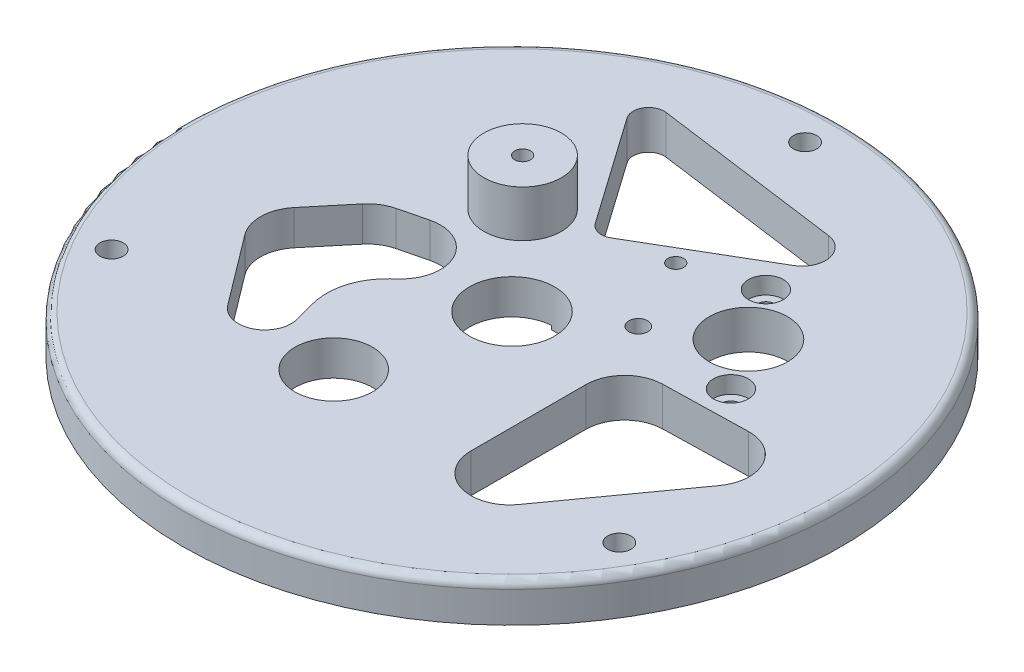
SolidWorks part; units mm, degrees
ref_plane "Front Plane" through (0, 0, 0) normal (0, 0, 1) x (1, 0, 0)
ref_plane "Top Plane" through (0, 0, 0) normal (0, 1, 0) x (1, 0, 0)
ref_plane "Right Plane" through (0, 0, 0) normal (1, 0, 0) x (0, 0, -1)
sketch "Sketch1" plane through (0, 0, 0) normal (0, 1, 0) x (1, 0, 0)
  circle A0 centre (0, 0) radius 42.5
  circle A9 centre (-5.0091, -17.9813) radius 5
  dimension "D1" = 85
  dimension "D5" = 10
  dimension "D6" = 18.666
extrude "Boss-Extrude1" add sketch "Sketch1" along normal blind 5
sketch "Sketch2" plane through (0, 5, 0) normal (0, 1, 0) x (1, 0, 0)
  line L0 (22.7613, 5.4702) -> (13.9311, 18.8129) construction
  line L1 (22.7613, 5.4702) -> (9.8011, 6.4864) construction
  line L2 (9.8011, 6.4864) -> (13.9311, 18.8129) construction
  line L3 (9.8011, 6.4864) -> (18.3462, 12.1416) construction
  circle A0 centre (22.7613, 5.4702) radius 1.2
  circle A1 centre (13.9311, 18.8129) radius 1.2
  circle A2 centre (9.8011, 6.4864) radius 1.225
  circle A3 centre (18.3462, 12.1416) radius 5.05
  circle A4 centre (5.1411, 15.9741) radius 1.015
  circle A5 centre (18.3462, 12.1416) radius 13.75 construction
  circle A6 centre (0, 0) radius 30 construction
  circle A7 centre (5.1411, 15.9741) radius 11.25 construction
  point P9 (18.3462, 12.1416)
  dimension "D1" = 2.4
  dimension "D2" = 10.1
  dimension "D3" = 2.45
  dimension "D7" = 2.03
  dimension "D9" = 60
  dimension "D10" = 22.5
  dimension "D4" = 16
  dimension "D5" = 13
  dimension "D6" = 22
  dimension "D8" = 13.75
extrude "Cut-Extrude1" cut sketch "Sketch2" against normal blind 10
sketch "Sketch4" plane through (0, 5, 0) normal (0, 1, 0) x (1, 0, 0)
  circle A0 centre (0, 0) radius 31 construction
  dimension "D1" = 62
sketch "Sketch5" plane through (0, 5, 0) normal (0, 1, 0) x (1, 0, 0)
  line L0 (-10.7483, 12.1208) -> (0, 0) construction
  circle A0 centre (-10.7483, 12.1208) radius 5
  circle A1 centre (5.1411, 15.9741) radius 1 construction
  circle A2 centre (-10.7483, 12.1208) radius 1.015
  circle A3 centre (-10.7483, 12.1208) radius 14 construction
  dimension "D2" = 10
  dimension "D3" = 2.03
  dimension "D4" = 28
  dimension "D1" = 16.35
  dimension "D5" = 16.2
extrude "Boss-Extrude2" add sketch "Sketch5" along normal blind 6
sketch "Sketch9" plane through (0, 0, 0) normal (0, -1, 0) x (1, 0, 0)
  circle A0 centre (5.1411, -15.9741) radius 2.3573
extrude "Boss-Extrude4" add sketch "Sketch9" against normal blind 1
fillet "Fillet1" radius 1 1 edges at (0, 5, 42.5)
sketch "Sketch10" plane through (0, 5, 0) normal (0, 1, 0) x (1, 0, 0)
  line L0 (-32.7358, -18.9) -> (0, 0) construction
  line L1 (0, 37.8) -> (0, 0) construction
  line L2 (32.7358, -18.9) -> (0, 0) construction
  circle A0 centre (0, 37.8) radius 1.5
  circle A1 centre (-32.7358, -18.9) radius 1.5
  circle A2 centre (32.7358, -18.9) radius 1.5
  dimension "D2" = 3
  dimension "D3" = 120
  dimension "D1" = 37.8
  dimension "D4" = 120
extrude "Cut-Extrude3" cut sketch "Sketch10" against normal blind 16 and the other way blind 2.2
sketch "Sketch12" plane through (0, 0, 0) normal (0, -1, 0) x (1, 0, 0)
  line L0 (-18.749, 25.6831) -> (-31.974, 2.7768)
  line L1 (-30.1438, -4.0534) -> (-11.5243, -14.8034)
  line L2 (-4.6942, -12.9732) -> (8.5308, 9.9331)
  line L3 (8.5308, 9.9331) -> (-18.749, 25.6831) construction
  line L4 (-5.1091, 17.8081) -> (-5.0091, 17.9813) construction
  line L5 (-32.7358, 18.9) -> (-36.8061, 21.25) construction
  line L6 (-25.1829, 14.5393) -> (-32.7358, 18.9) construction
  line L7 (-35.4958, 23.5194) -> (-39.334, 16.8715) construction
  arc A0 (-18.749, 25.6831) -> (8.5308, 9.9331) centre (-5.1091, 17.8081) cw
  arc A1 (-4.6942, -12.9732) -> (-11.5243, -14.8034) centre (-9.0243, -10.4732) cw
  arc A2 (-31.974, 2.7768) -> (-30.1438, -4.0534) centre (-27.6438, 0.2768) ccw
  circle A3 centre (-5.0091, 17.9813) radius 4.1018 construction
  circle A4 centre (-5.0091, 17.9813) radius 5 construction
  circle A5 centre (0, 0) radius 42.5 construction
  point P4 (2.7659, 31.448)
  point P9 (-7.1942, -17.3034)
  point P12 (-34.474, -1.5534)
  point P24 (0, 0)
  point P25 (-27.6438, 0)
  point P26 (-27.6438, 0)
  dimension "D3" = 5
  dimension "D4" = 0.2
  dimension "D1" = 47.2
  dimension "D2" = 31.5
extrude "Cut-Extrude6" cut sketch "Sketch12" against normal blind 0.5
sketch "Sketch13" plane through (0, 5, 0) normal (0, 1, 0) x (1, 0, 0)
  line L0 (32.8168, -6.0717) -> (21.985, -21.1386)
  line L1 (12.9252, -18.2178) -> (12.9317, -3.4072)
  line L2 (17.8133, 1.5892) -> (28.6387, 1.8455)
  arc A0 (21.985, -21.1386) -> (12.9252, -18.2178) centre (17.9252, -18.22) cw
  arc A1 (17.8133, 1.5892) -> (12.9317, -3.4072) centre (17.9317, -3.4094) ccw
  arc A2 (28.6387, 1.8455) -> (32.8168, -6.0717) centre (28.7571, -3.1531) cw
  dimension "D1" = 5
extrude "Cut-Extrude7" cut sketch "Sketch13" against normal blind 10
sketch "Sketch15" plane through (0, 0.5, 0) normal (0, -1, 0) x (1, 0, 0)
  line L0 (-4.4541, -15.187) -> (-14.1901, -29.0283)
  line L1 (-12.2862, -32.1609) -> (11.9263, -28.8867)
  line L2 (13.0439, -23.3011) -> (-1.8082, -14.6114)
  arc A0 (-4.4541, -15.187) -> (-1.8082, -14.6114) centre (-2.8182, -16.3376) cw
  arc A1 (-12.2862, -32.1609) -> (-14.1901, -29.0283) centre (-12.5542, -30.1789) cw
  arc A2 (11.9263, -28.8867) -> (13.0439, -23.3011) centre (11.5226, -25.9013) ccw
  dimension "D1" = 2
extrude "Cut-Extrude8" cut sketch "Sketch15" against normal blind 10 and the other way blind 10
sketch "Sketch16" plane through (0, 0.5, 0) normal (0, -1, 0) x (1, 0, 0)
  line L0 (-12.9842, 14.7056) -> (-13.7197, 11.9588)
  line L1 (-11.5496, 4.2419) -> (-10.8428, 3.5689)
  line L2 (-15.4939, -4.9052) -> (-19.0041, -4.0349)
  line L3 (-21.6454, -2.3787) -> (-25.6533, 2.4414)
  line L4 (-25.8003, 8.6495) -> (-19.0121, 17.6471)
  arc A0 (-25.6533, 2.4414) -> (-25.8003, 8.6495) centre (-21.8088, 5.6382) cw
  arc A1 (-19.0041, -4.0349) -> (-21.6454, -2.3787) centre (-17.8008, 0.8181) cw
  arc A2 (-15.4939, -4.9052) -> (-10.8428, 3.5689) centre (-14.2907, -0.0522) ccw
  arc A3 (-13.7197, 11.9588) -> (-11.5496, 4.2419) centre (-6.1357, 9.9279) ccw
  arc A4 (-12.9842, 14.7056) -> (-19.0121, 17.6471) centre (-16.2845, 15.5894) ccw
  point P15 (-14.4378, 0)
  point P16 (-14.4378, 12.8998)
  point P17 (-8.2451, -4.407)
  point P18 (-17.3042, -6.2007)
  point P19 (-5.7331, -4.8881)
  point P20 (0, 0)
  point P21 (-10.9048, -2.1941)
  point P22 (-23.2964, -4.5725)
  point P23 (-13.4335, -7.2999)
  point P24 (-26.4724, 1.6715)
  point P25 (-18.6835, -0.8933)
  point P26 (-11.5496, 4.2419)
  point P27 (-16.2845, 15.5894)
  point P28 (-17.8008, 0.8181)
  dimension "D1" = 5
extrude "Cut-Extrude9" cut sketch "Sketch16" against normal blind 10 and the other way blind 10
sketch "Sketch17" plane through (0, 0.5, 0) normal (0, -1, 0) x (1, 0, 0)
  circle A0 centre (0, 0) radius 5.5
  dimension "D1" = 11
extrude "Cut-Extrude10" cut sketch "Sketch17" against normal blind 10 and the other way blind 10
sketch "Sketch18" plane through (0, 5, 0) normal (0, 1, 0) x (1, 0, 0)
  circle A0 centre (13.9311, 18.8129) radius 2.25
  circle A1 centre (22.7613, 5.4702) radius 2.25
  dimension "D1" = 4.5
extrude "Cut-Extrude11" cut sketch "Sketch18" against normal blind 2.2
